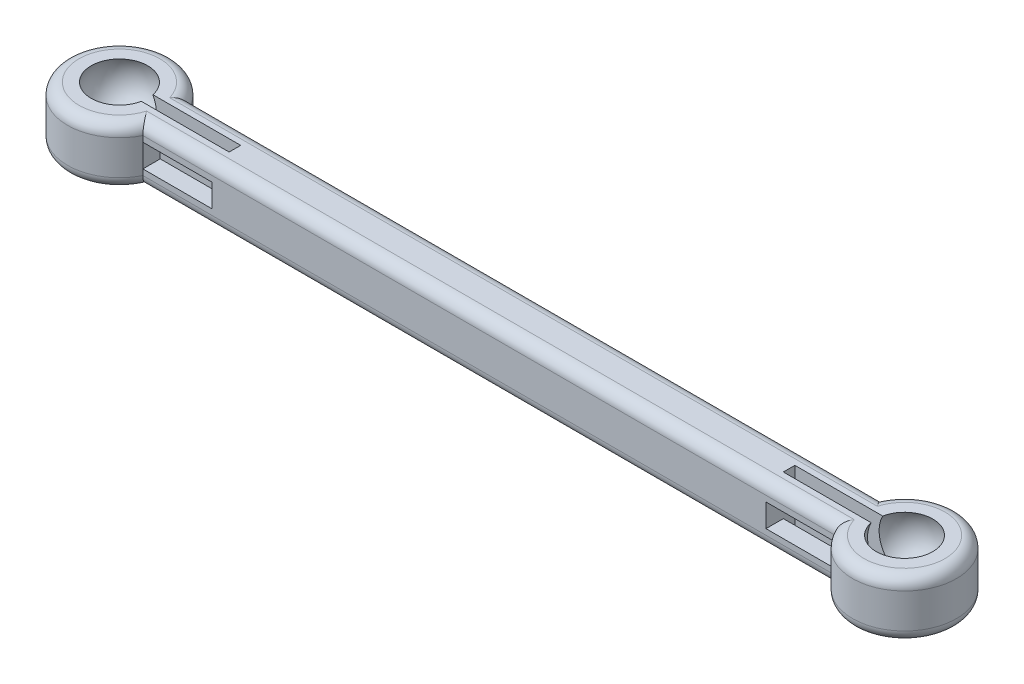
SolidWorks part; units mm, degrees
ref_plane "Front Plane" through (0, 0, 0) normal (0, 0, 1) x (1, 0, 0)
ref_plane "Top Plane" through (0, 0, 0) normal (0, 1, 0) x (1, 0, 0)
ref_plane "Right Plane" through (0, 0, 0) normal (1, 0, 0) x (0, 0, -1)
sketch "Sketch1" plane through (0, 0, 0) normal (0, 1, 0) x (1, 0, 0)
  line L1 (-34, -2) -> (34, -2)
  line L2 (-34, -2) -> (-34, 2)
  line L3 (-34, 2) -> (34, 2)
  line L4 (34, -2) -> (34, 2)
  line L5 (-34, -2) -> (34, 2) construction
  line L6 (-34, 2) -> (34, -2) construction
  circle A0 centre (34, 0) radius 4.5
  circle A1 centre (-34, 0) radius 4.5
  point P0 (0, 0)
  point P4 (0, 0)
  dimension "D2" = 9
  dimension "D1" = 68
  dimension "D3" = 4
extrude "Boss-Extrude1" add sketch "Sketch1" along normal blind 5 contours L3 A1 L1 L2 | L1 A1 L3 L2 | A1 L1 A0 L3 | L3 A0 L1 L4 | L1 A0 L3 L4
sketch3d "3DSketch1"
  line L0 (-34, 5, 0) -> (-34, 6.5, 0)
  line L1 (-34, 5, 0) -> (-34, 1, 0)
  arc A0 (-29.9689, 5, -2) -> (-29.9689, 5, 2) centre (-34, 5, 0) ccw construction
  arc A1 (-34, 1, 0) -> (-34, 6.5, 0) centre (-34, 3.75, 0) cw
  point P3 (-36.75, 3.75, 0)
  point P7 (-34, 9.5, 0)
  dimension "D1" = 4
  dimension "D2" = 1.5
sketch "Sketch2" plane through (0, 5, 0) normal (0, 1, 0) x (1, 0, 0)
  circle A0 centre (-34, 0) radius 4.5
  arc A1 (-29.9689, 2) -> (-29.9689, -2) centre (-34, 0) ccw construction
sweep "Cut-Sweep1" cut profiles "3DSketch1" path "Sketch2"
mirror "Mirror1" about plane through (0, 0, 0) normal (1, 0, 0) of "Cut-Sweep1"
sketch "Sketch3" plane through (0, 0, 0) normal (0, -1, 0) x (1, 0, 0)
  line L0 (-29.9689, 2) -> (29.9689, 2) construction
  line L1 (-34, 0) -> (-24, 0)
  line L2 (-34, 0) -> (-34, 0.5)
  line L3 (-34, 0.5) -> (-24, 0.5)
  line L4 (-24, 0) -> (-24, 0.5)
  line L5 (-34, 0) -> (-24, 0)
  line L6 (-34, 0) -> (-34, -0.5)
  line L7 (-34, -0.5) -> (-24, -0.5)
  line L8 (-24, 0) -> (-24, -0.5)
  circle A0 centre (-34, 0) radius 4.5
  arc A1 (-29.9689, 2) -> (-29.9689, -2) centre (-34, 0) ccw construction
  dimension "D1" = 1.5
  dimension "D2" = 10
extrude "Cut-Extrude1" cut sketch "Sketch3" against normal up to surface (5 mm away) contours A0 L5 L4 L3 | A0 L7 L8 L5 | L1 A0 L3 L2 | L7 A0 L1 L6 up to face at (34, 5, 2.4495)
mirror "Mirror2" about plane through (0, 0, 0) normal (1, 0, 0) of "Cut-Extrude1"
sketch "Sketch4" plane through (0, 0, -2) normal (0, 0, -1) x (-1, 0, 0)
  line L0 (29.9689, 0) -> (24, 5)
  line L2 (29.9689, 5) -> (-29.9689, 5) construction
  line L3 (29.9689, 5) -> (29.9689, 0) construction
  line L4 (29.9689, 3.5) -> (24, 3.5)
  line L5 (29.9689, 3.5) -> (29.9689, 1.5)
  line L6 (29.9689, 1.5) -> (24, 1.5)
  line L7 (24, 3.5) -> (24, 1.5)
  line L8 (29.9689, 3.5) -> (24, 1.5) construction
  line L9 (29.9689, 1.5) -> (24, 3.5) construction
  point P6 (26.9844, 2.5)
  line M6 (29.9689, 0) -> (29.9689, 5)
  dimension "D1" = 2
extrude "Cut-Extrude2" cut sketch "Sketch4" against normal up to surface (4 mm away) contours L4 L7 L6 L0 | L6 L4 L0 M6 up to face at (0, 2.5, 2)
mirror "Mirror3" about plane through (0, 0, 0) normal (1, 0, 0) of "Cut-Extrude2"
fillet "Fillet1" radius 1 8 edges at (-38.5, 0, 0) (-38.5, 5, 0) (0, 5, 2) (0, 0, 2) (0, 0, -2) (0, 5, -2) (38.5, 0, 0) (38.5, 5, 0)
